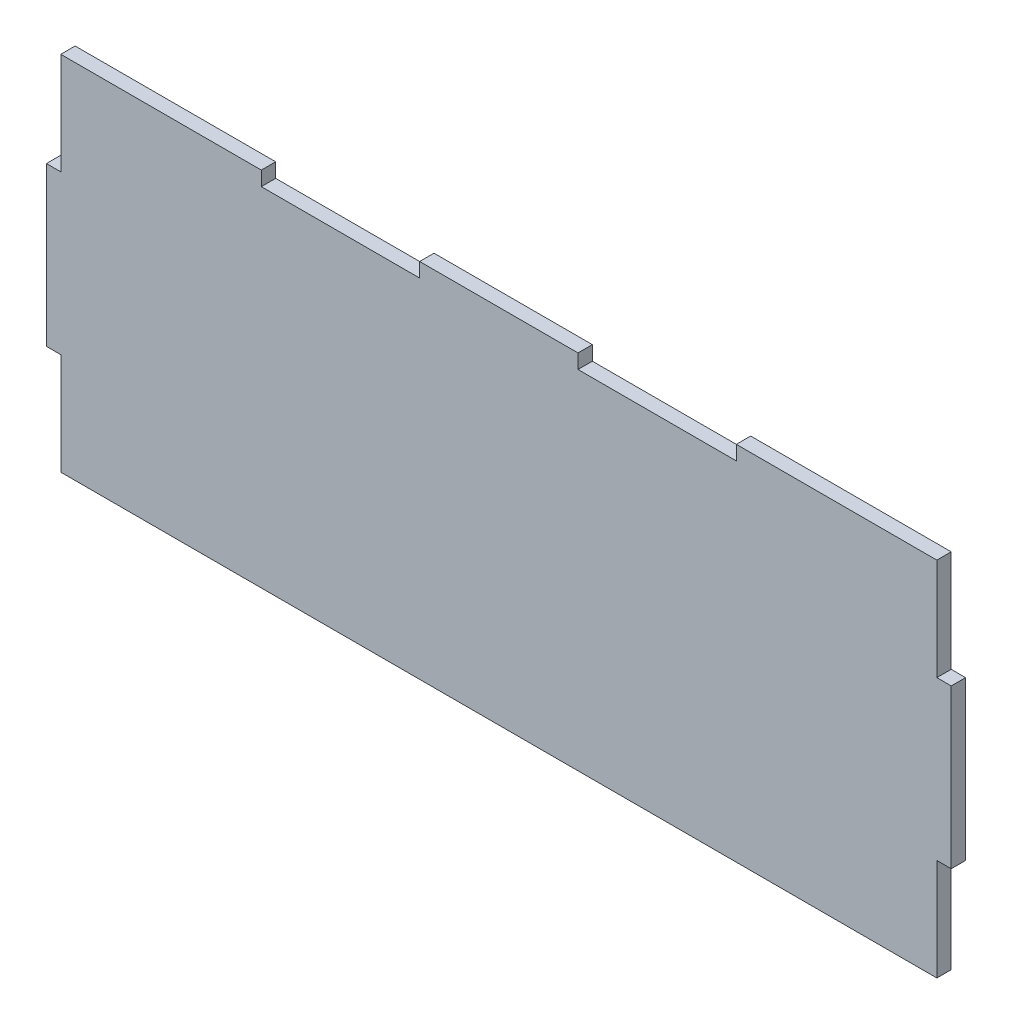
SolidWorks part; units mm, degrees
ref_plane "Plan de face" through (0, 0, 0) normal (0, 0, 1) x (1, 0, 0)
ref_plane "Plan de dessus" through (0, 0, 0) normal (0, 1, 0) x (1, 0, 0)
ref_plane "Plan de droite" through (0, 0, 0) normal (1, 0, 0) x (0, 0, -1)
sketch "Esquisse2" plane through (0, 0, 0) normal (0, 0, 1) x (1, 0, 0)
  line L1 (-100, 40) -> (100, 40)
  line L2 (-100, 40) -> (-100, -40)
  line L3 (-100, -40) -> (100, -40)
  line L4 (100, 40) -> (100, -40)
  point P4 (0, 40)
  point P6 (100, 0)
  dimension "D1" = 200
  dimension "D2" = 80
extrude "Boss.-Extru.1" add sketch "Esquisse2" along normal blind 3.175
sketch "Esquisse3" plane through (0, 0, 3.175) normal (0, 0, 1) x (1, 0, 0)
  line L0 (100, 40) -> (-100, 40) construction
  line L1 (17.5, 40) -> (52.5, 40)
  line L2 (17.5, 40) -> (17.5, 36.825)
  line L3 (17.5, 36.825) -> (52.5, 36.825)
  line L4 (52.5, 40) -> (52.5, 36.825)
  line L6 (-17.5, 40) -> (-52.5, 40)
  line L7 (-17.5, 40) -> (-17.5, 36.825)
  line L8 (-17.5, 36.825) -> (-52.5, 36.825)
  line L9 (-52.5, 40) -> (-52.5, 36.825)
  dimension "D1" = 3.175
  dimension "D2" = 3.175
  dimension "D3" = 35
  dimension "D4" = 35
  dimension "D5" = 35
  dimension "D6" = 17.5
extrude "Enlèv. mat.-Extru.1" cut sketch "Esquisse3" against normal through all
sketch "Esquisse4" plane through (0, 0, 3.175) normal (0, 0, 1) x (1, 0, 0)
  line L1 (-100, 40) -> (-96.825, 40)
  line L2 (-100, 40) -> (-100, 17.5)
  line L3 (-100, 17.5) -> (-96.825, 17.5)
  line L4 (-96.825, 40) -> (-96.825, 17.5)
  line L5 (-100, -40) -> (-96.825, -40)
  line L6 (-100, -40) -> (-100, -17.5)
  line L7 (-100, -17.5) -> (-96.825, -17.5)
  line L8 (-96.825, -40) -> (-96.825, -17.5)
  dimension "D1" = 3.175
  dimension "D2" = 3.175
  dimension "D3" = 35
extrude "Enlèv. mat.-Extru.2" cut sketch "Esquisse4" against normal through all
mirror "Symétrie1" about plane through (0, 0, 0) normal (1, 0, 0) of "Enlèv. mat.-Extru.2"
